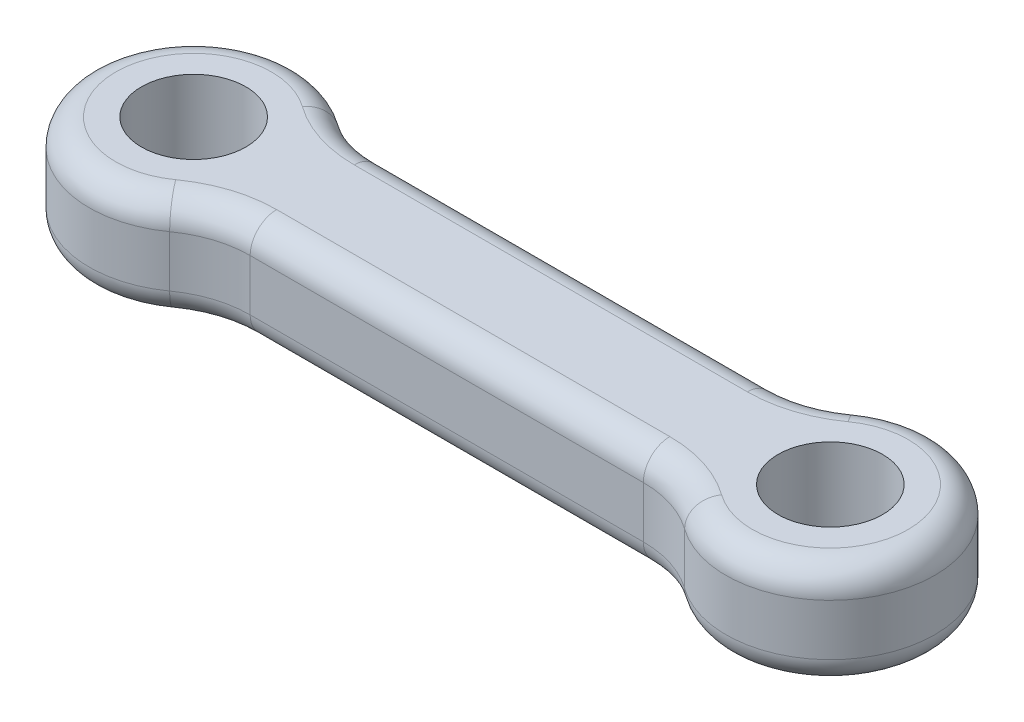
SolidWorks part; units mm, degrees
ref_plane "Front Plane" through (0, 0, 0) normal (0, 0, 1) x (1, 0, 0)
ref_plane "Top Plane" through (0, 0, 0) normal (0, 1, 0) x (1, 0, 0)
ref_plane "Right Plane" through (0, 0, 0) normal (1, 0, 0) x (0, 0, -1)
sketch "Sketch1" plane through (0, 0, 0) normal (0, 1, 0) x (1, 0, 0)
  line L0 (-15.24, 0) -> (15.24, 0) construction
  line L1 (-3.5808, -6.25) -> (34.0608, -6.25)
  line L2 (-3.5808, 6.25) -> (34.0608, 6.25)
  line L3 (-9.4104, -8.125) -> (-9.4104, 8.125) construction
  line L4 (-3.5808, -6.25) -> (-3.5808, 6.25) construction
  line L5 (15.24, -6.25) -> (15.24, 6.25) construction
  arc A0 (-9.4104, 8.125) -> (-9.4104, -8.125) centre (-15.24, 0) ccw
  arc A1 (-9.4104, -8.125) -> (-3.5808, -6.25) centre (-3.5808, -16.25) cw
  arc A2 (-9.4104, 8.125) -> (-3.5808, 6.25) centre (-3.5808, 16.25) ccw
  circle A3 centre (-15.24, 0) radius 5
  circle A4 centre (45.72, 0) radius 5
  arc A5 (39.8904, -8.125) -> (34.0608, -6.25) centre (34.0608, -16.25) ccw
  arc A6 (39.8904, 8.125) -> (39.8904, -8.125) centre (45.72, 0) cw
  arc A7 (39.8904, 8.125) -> (34.0608, 6.25) centre (34.0608, 16.25) cw
  dimension "D3" = 10
  dimension "D4" = 12.5
  dimension "D5" = 10
  dimension "D2" = 10
  dimension "D1" = 30.48
extrude "Boss-Extrude1" add sketch "Sketch1" along normal blind 10
fillet "Fillet1" radius 2.54 16 edges at (-25.24, 0, 0) (-6.6426, 0, 6.7303) (15.24, 0, 6.25) (37.1226, 0, 6.7303) (55.72, 0, 0) (37.1226, 0, -6.7303) (15.24, 0, -6.25) (-6.6426, 0, -6.7303) (15.24, 10, -6.25) (37.1226, 10, -6.7303) (55.72, 10, 0) (37.1226, 10, 6.7303) (15.24, 10, 6.25) (-6.6426, 10, 6.7303) (-25.24, 10, 0) (-6.6426, 10, -6.7303)
scale "Scale1" scale about centroid uniform scaling yes scale factor 0.66
